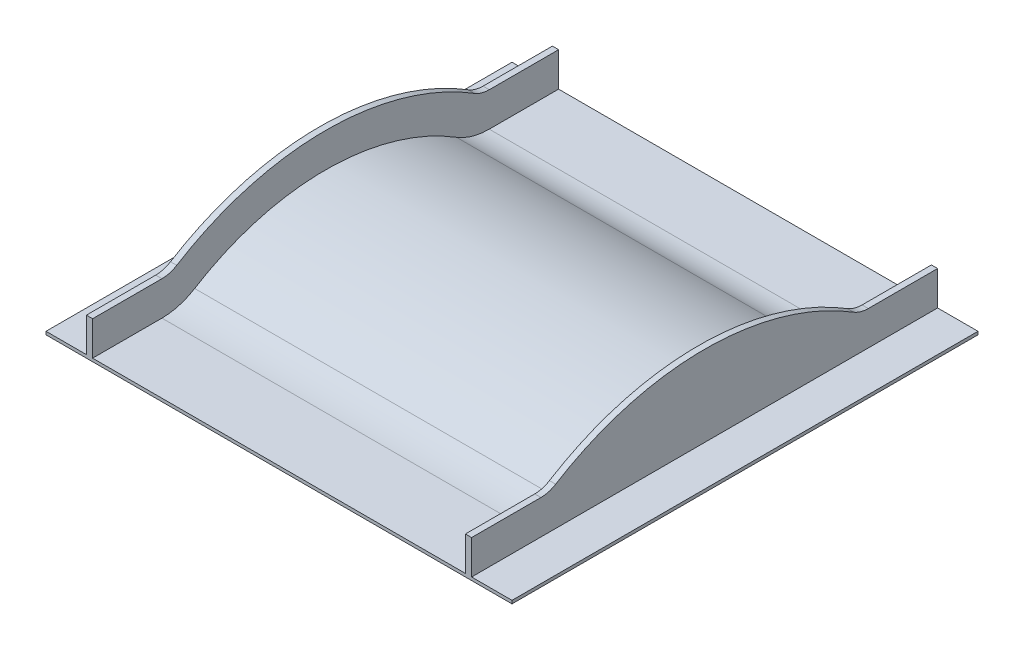
SolidWorks part; units mm, degrees
ref_plane "Front Plane" through (0, 0, 0) normal (0, 0, 1) x (1, 0, 0)
ref_plane "Top Plane" through (0, 0, 0) normal (0, 1, 0) x (1, 0, 0)
ref_plane "Right Plane" through (0, 0, 0) normal (1, 0, 0) x (0, 0, -1)
sketch "Sketch2" plane through (0, 0, 0) normal (0, 1, 0) x (1, 0, 0)
  line L1 (-750, 750) -> (750, 750)
  line L2 (-750, 750) -> (-750, -750)
  line L3 (-750, -750) -> (750, -750)
  line L4 (750, 750) -> (750, -750)
  line L5 (-750, 750) -> (750, -750) construction
  line L6 (-750, -750) -> (750, 750) construction
  point P0 (0, 0)
  dimension "D1" = 1500
  dimension "D2" = 1500
extrude "Boss-Extrude1" add sketch "Sketch2" along normal blind 10
ref_plane "Plane1" through (-620, 0, 0) normal (-1, 0, 0) x (0, 0, 1)
sketch "Sketch4" plane through (-620, 0, 0) normal (-1, 0, 0) x (0, 0, 1)
  line L0 (0, 10) -> (0, 160) construction
  line L1 (-750, 10) -> (750, 10) construction
  line L2 (-750, 160) -> (750, 160) construction
  line L3 (-526.7827, 10) -> (526.7827, 10)
  circle A0 centre (0, -640) radius 800
  circle A1 centre (526.7827, 210) radius 200
  circle A2 centre (-526.7827, 210) radius 200
  dimension "D2" = 1600
  dimension "D3" = 400
  dimension "D1" = 150
extrude "Boss-Extrude3" add sketch "Sketch4" against normal offset from surface (1240 mm away) 130
sketch "Sketch3" plane through (0, 10, 0) normal (0, 1, 0) x (1, 0, 0)
  line L0 (620, 750) -> (620, -750) construction
  line L1 (750, 750) -> (-750, 750) construction
  line L2 (-750, -750) -> (750, -750) construction
  line L3 (600, 750) -> (600, -750) construction
  line L4 (750, -750) -> (750, 750) construction
  line L5 (-750, -600) -> (750, -600) construction
  line L6 (-750, 750) -> (-750, -750) construction
  line L7 (-750, -620) -> (750, -620) construction
  line L8 (-750, 0) -> (750, 0) construction
  line L9 (0, 750) -> (0, -750) construction
  line L10 (-750, 620) -> (750, 620) construction
  line L11 (-750, 600) -> (750, 600) construction
  line L12 (-620, 750) -> (-620, -750) construction
  line L13 (-600, 750) -> (-600, -750) construction
  line L15 (-620, 750) -> (-600, 750)
  line L16 (-620, 750) -> (-620, -750)
  line L17 (-620, -750) -> (-600, -750)
  line L18 (-600, 750) -> (-600, -750)
  line L19 (600, 750) -> (620, 750)
  line L20 (600, 750) -> (600, -750)
  line L21 (600, -750) -> (620, -750)
  line L22 (620, 750) -> (620, -750)
  dimension "D6" = 150
  dimension "D5" = 20
  dimension "D7" = 20
  dimension "D8" = 150
sketch "Sketch5" plane through (-620, 0, 0) normal (-1, 0, 0) x (0, 0, 1)
  line L0 (-750, 10) -> (750, 10) construction
  line L1 (-750, 10) -> (750, 10)
  line L2 (-750, 120) -> (750, 120)
  line L3 (-750, 120) -> (-750, 10)
  line L4 (750, 120) -> (750, 10)
  arc A0 (421.4262, 40) -> (526.7827, 10) centre (526.7827, 210) ccw construction
  arc A1 (421.4262, 40) -> (-421.4262, 40) centre (0, -640) ccw construction
  arc A2 (-526.7827, 10) -> (-421.4262, 40) centre (-526.7827, 210) ccw construction
  arc A3 (421.4262, 40) -> (526.7827, 10) centre (526.7827, 210) ccw
  arc A4 (421.4262, 40) -> (-421.4262, 40) centre (0, -640) ccw
  arc A5 (-526.7827, 10) -> (-421.4262, 40) centre (-526.7827, 210) ccw
  arc A6 (-526.7827, 120) -> (-479.3722, 133.5) centre (-526.7827, 210) ccw
  arc A7 (479.3722, 133.5) -> (-479.3722, 133.5) centre (0, -640) ccw
  arc A8 (479.3722, 133.5) -> (526.7827, 120) centre (526.7827, 210) ccw
  dimension "D1" = 110
extrude "Boss-Extrude4" add sketch "Sketch5" against normal blind 20 contours L1 A5 A4 L2 L3 | A8 A7 A6 L2 A4 | A4 A3 L1 L4 L2
mirror "Mirror1" about plane through (0, 0, 0) normal (1, 0, 0) of "Boss-Extrude4"
equation "\"CellSize\"=1500"
equation "\"D1@Sketch2\"=\"CellSize\""
equation "\"D2@Sketch2\"=\"CellSize\""
equation "\"TrackWidth\"= 1200"
equation "\"C\"=342.079"
equation "\"WallWidth\"=20"
equation "\"D6@Sketch3\"=\"EdgeWidth\""
equation "\"D5@Sketch3\"=\"WallWidth\""
equation "\"D7@Sketch3\"=\"WallWidth\""
equation "\"EdgeWidth\"= ( \"CellSize\" - \"TrackWidth\" ) / 2"
equation "\"D8@Sketch3\"=\"EdgeWidth\""
